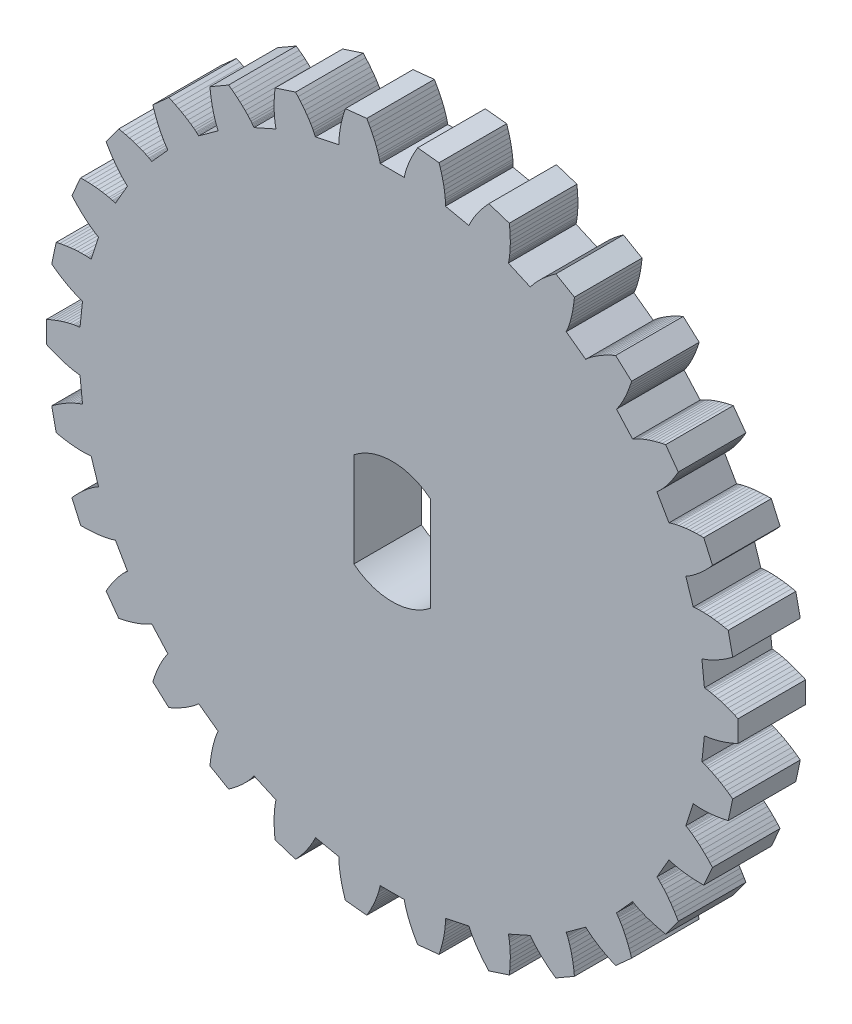
SolidWorks part; units mm, degrees
ref_plane "Front Plane" through (0, 0, 0) normal (0, 0, 1) x (1, 0, 0)
ref_plane "Top Plane" through (0, 0, 0) normal (0, 1, 0) x (1, 0, 0)
ref_plane "Right Plane" through (0, 0, 0) normal (1, 0, 0) x (0, 0, -1)
sketch "Model" plane through (0, 0, 0) normal (0, 0, 1) x (1, 0, 0)
  line L0 (29.209, 16.2732) -> (29.246, 16.2699)
  line L1 (29.246, 16.2699) -> (29.2831, 16.266)
  line L2 (29.2831, 16.266) -> (29.3202, 16.2615)
  line L3 (29.3202, 16.2615) -> (29.3573, 16.2565)
  line L4 (29.3573, 16.2565) -> (29.4317, 16.245)
  line L5 (29.4317, 16.245) -> (29.5061, 16.2317)
  line L6 (29.5061, 16.2317) -> (29.6552, 16.2001)
  line L7 (29.6552, 16.2001) -> (29.8045, 16.1625)
  line L8 (29.8045, 16.1625) -> (29.954, 16.1194)
  line L9 (29.954, 16.1194) -> (30.1035, 16.0712)
  line L10 (30.1035, 16.0712) -> (30.2531, 16.0181)
  line L11 (30.2531, 16.0181) -> (30.4025, 15.9603)
  line L12 (30.4025, 15.9603) -> (30.5519, 15.8981)
  line L13 (30.5519, 15.8981) -> (30.7012, 15.8315)
  line L14 (30.7012, 15.8315) -> (30.7012, 14.8771)
  line L15 (30.7012, 14.8771) -> (30.5519, 14.8105)
  line L16 (30.5519, 14.8105) -> (30.4025, 14.7482)
  line L17 (30.4025, 14.7482) -> (30.2531, 14.6905)
  line L18 (30.2531, 14.6905) -> (30.1035, 14.6374)
  line L19 (30.1035, 14.6374) -> (29.954, 14.5891)
  line L20 (29.954, 14.5891) -> (29.8045, 14.5461)
  line L21 (29.8045, 14.5461) -> (29.6552, 14.5085)
  line L22 (29.6552, 14.5085) -> (29.5061, 14.4769)
  line L23 (29.5061, 14.4769) -> (29.4317, 14.4636)
  line L24 (29.4317, 14.4636) -> (29.3573, 14.4521)
  line L25 (29.3573, 14.4521) -> (29.3202, 14.4471)
  line L26 (29.3202, 14.4471) -> (29.2831, 14.4426)
  line L27 (29.2831, 14.4426) -> (29.246, 14.4387)
  line L28 (29.246, 14.4387) -> (29.209, 14.4354)
  line L29 (29.209, 14.4354) -> (29.0973, 13.3725)
  line L30 (29.0973, 13.3725) -> (29.1328, 13.3616)
  line L31 (29.1328, 13.3616) -> (29.1683, 13.3501)
  line L32 (29.1683, 13.3501) -> (29.2036, 13.338)
  line L33 (29.2036, 13.338) -> (29.2389, 13.3254)
  line L34 (29.2389, 13.3254) -> (29.3092, 13.2987)
  line L35 (29.3092, 13.2987) -> (29.3793, 13.2702)
  line L36 (29.3793, 13.2702) -> (29.5185, 13.2083)
  line L37 (29.5185, 13.2083) -> (29.6568, 13.1405)
  line L38 (29.6568, 13.1405) -> (29.794, 13.0673)
  line L39 (29.794, 13.0673) -> (29.9303, 12.989)
  line L40 (29.9303, 12.989) -> (30.0655, 12.906)
  line L41 (30.0655, 12.906) -> (30.1997, 12.8184)
  line L42 (30.1997, 12.8184) -> (30.3329, 12.7264)
  line L43 (30.3329, 12.7264) -> (30.465, 12.6303)
  line L44 (30.465, 12.6303) -> (30.2666, 11.6967)
  line L45 (30.2666, 11.6967) -> (30.1068, 11.6626)
  line L46 (30.1068, 11.6626) -> (29.9477, 11.6328)
  line L47 (29.9477, 11.6328) -> (29.7895, 11.6074)
  line L48 (29.7895, 11.6074) -> (29.6321, 11.5865)
  line L49 (29.6321, 11.5865) -> (29.4759, 11.5704)
  line L50 (29.4759, 11.5704) -> (29.3207, 11.5594)
  line L51 (29.3207, 11.5594) -> (29.1668, 11.5536)
  line L52 (29.1668, 11.5536) -> (29.0144, 11.5537)
  line L53 (29.0144, 11.5537) -> (28.9389, 11.5562)
  line L54 (28.9389, 11.5562) -> (28.8637, 11.5604)
  line L55 (28.8637, 11.5604) -> (28.8264, 11.5632)
  line L56 (28.8264, 11.5632) -> (28.7892, 11.5666)
  line L57 (28.7892, 11.5666) -> (28.7521, 11.5704)
  line L58 (28.7521, 11.5704) -> (28.7152, 11.5749)
  line L59 (28.7152, 11.5749) -> (28.3849, 10.5585)
  line L60 (28.3849, 10.5585) -> (28.4174, 10.5404)
  line L61 (28.4174, 10.5404) -> (28.4497, 10.5218)
  line L62 (28.4497, 10.5218) -> (28.4818, 10.5026)
  line L63 (28.4818, 10.5026) -> (28.5137, 10.4829)
  line L64 (28.5137, 10.4829) -> (28.5769, 10.4422)
  line L65 (28.5769, 10.4422) -> (28.6395, 10.3998)
  line L66 (28.6395, 10.3998) -> (28.7628, 10.3103)
  line L67 (28.7628, 10.3103) -> (28.884, 10.2152)
  line L68 (28.884, 10.2152) -> (29.003, 10.115)
  line L69 (29.003, 10.115) -> (29.12, 10.0102)
  line L70 (29.12, 10.0102) -> (29.235, 9.9008)
  line L71 (29.235, 9.9008) -> (29.3481, 9.7873)
  line L72 (29.3481, 9.7873) -> (29.4592, 9.6696)
  line L73 (29.4592, 9.6696) -> (29.5684, 9.5481)
  line L74 (29.5684, 9.5481) -> (29.1802, 8.6762)
  line L75 (29.1802, 8.6762) -> (29.0168, 8.6761)
  line L76 (29.0168, 8.6761) -> (28.8551, 8.68)
  line L77 (28.8551, 8.68) -> (28.695, 8.688)
  line L78 (28.695, 8.688) -> (28.5368, 8.7003)
  line L79 (28.5368, 8.7003) -> (28.3806, 8.7171)
  line L80 (28.3806, 8.7171) -> (28.2265, 8.7385)
  line L81 (28.2265, 8.7385) -> (28.0748, 8.7649)
  line L82 (28.0748, 8.7649) -> (27.9257, 8.7967)
  line L83 (27.9257, 8.7967) -> (27.8523, 8.8148)
  line L84 (27.8523, 8.8148) -> (27.7797, 8.8345)
  line L85 (27.7797, 8.8345) -> (27.7438, 8.8451)
  line L86 (27.7438, 8.8451) -> (27.7081, 8.8561)
  line L87 (27.7081, 8.8561) -> (27.6726, 8.8676)
  line L88 (27.6726, 8.8676) -> (27.6375, 8.8796)
  line L89 (27.6375, 8.8796) -> (27.1031, 7.9541)
  line L90 (27.1031, 7.9541) -> (27.1311, 7.9296)
  line L91 (27.1311, 7.9296) -> (27.1588, 7.9047)
  line L92 (27.1588, 7.9047) -> (27.1862, 7.8793)
  line L93 (27.1862, 7.8793) -> (27.2133, 7.8534)
  line L94 (27.2133, 7.8534) -> (27.2667, 7.8004)
  line L95 (27.2667, 7.8004) -> (27.3191, 7.7459)
  line L96 (27.3191, 7.7459) -> (27.4211, 7.6327)
  line L97 (27.4211, 7.6327) -> (27.5198, 7.5145)
  line L98 (27.5198, 7.5145) -> (27.6154, 7.3918)
  line L99 (27.6154, 7.3918) -> (27.708, 7.2649)
  line L100 (27.708, 7.2649) -> (27.7978, 7.134)
  line L101 (27.7978, 7.134) -> (27.8848, 6.9994)
  line L102 (27.8848, 6.9994) -> (27.9691, 6.8613)
  line L103 (27.9691, 6.8613) -> (28.0507, 6.7197)
  line L104 (28.0507, 6.7197) -> (27.4897, 5.9476)
  line L105 (27.4897, 5.9476) -> (27.3298, 5.9814)
  line L106 (27.3298, 5.9814) -> (27.1724, 6.0188)
  line L107 (27.1724, 6.0188) -> (27.0175, 6.06)
  line L108 (27.0175, 6.06) -> (26.8653, 6.1049)
  line L109 (26.8653, 6.1049) -> (26.7159, 6.1538)
  line L110 (26.7159, 6.1538) -> (26.5697, 6.2068)
  line L111 (26.5697, 6.2068) -> (26.4268, 6.2641)
  line L112 (26.4268, 6.2641) -> (26.2876, 6.3262)
  line L113 (26.2876, 6.3262) -> (26.2196, 6.3592)
  line L114 (26.2196, 6.3592) -> (26.1527, 6.3936)
  line L115 (26.1527, 6.3936) -> (26.1197, 6.4114)
  line L116 (26.1197, 6.4114) -> (26.0871, 6.4296)
  line L117 (26.0871, 6.4296) -> (26.0548, 6.4482)
  line L118 (26.0548, 6.4482) -> (26.0229, 6.4673)
  line L119 (26.0229, 6.4673) -> (25.3078, 5.6731)
  line L120 (25.3078, 5.6731) -> (25.3301, 5.6433)
  line L121 (25.3301, 5.6433) -> (25.352, 5.6132)
  line L122 (25.352, 5.6132) -> (25.3735, 5.5826)
  line L123 (25.3735, 5.5826) -> (25.3946, 5.5517)
  line L124 (25.3946, 5.5517) -> (25.4358, 5.4888)
  line L125 (25.4358, 5.4888) -> (25.4757, 5.4245)
  line L126 (25.4757, 5.4245) -> (25.552, 5.2926)
  line L127 (25.552, 5.2926) -> (25.624, 5.1565)
  line L128 (25.624, 5.1565) -> (25.692, 5.0166)
  line L129 (25.692, 5.0166) -> (25.7562, 4.8732)
  line L130 (25.7562, 4.8732) -> (25.8168, 4.7265)
  line L131 (25.8168, 4.7265) -> (25.8739, 4.5768)
  line L132 (25.8739, 4.5768) -> (25.9276, 4.4241)
  line L133 (25.9276, 4.4241) -> (25.978, 4.2687)
  line L134 (25.978, 4.2687) -> (25.2687, 3.63)
  line L135 (25.2687, 3.63) -> (25.1194, 3.6964)
  line L136 (25.1194, 3.6964) -> (24.9732, 3.7657)
  line L137 (24.9732, 3.7657) -> (24.8302, 3.8382)
  line L138 (24.8302, 3.8382) -> (24.6907, 3.9138)
  line L139 (24.6907, 3.9138) -> (24.5548, 3.9926)
  line L140 (24.5548, 3.9926) -> (24.4227, 4.0749)
  line L141 (24.4227, 4.0749) -> (24.2949, 4.1607)
  line L142 (24.2949, 4.1607) -> (24.1717, 4.2503)
  line L143 (24.1717, 4.2503) -> (24.112, 4.2968)
  line L144 (24.112, 4.2968) -> (24.0537, 4.3443)
  line L145 (24.0537, 4.3443) -> (24.0251, 4.3685)
  line L146 (24.0251, 4.3685) -> (23.997, 4.3931)
  line L147 (23.997, 4.3931) -> (23.9693, 4.4181)
  line L148 (23.9693, 4.4181) -> (23.9421, 4.4434)
  line L149 (23.9421, 4.4434) -> (23.0774, 3.8152)
  line L150 (23.0774, 3.8152) -> (23.0931, 3.7815)
  line L151 (23.0931, 3.7815) -> (23.1082, 3.7474)
  line L152 (23.1082, 3.7474) -> (23.1229, 3.7131)
  line L153 (23.1229, 3.7131) -> (23.1371, 3.6784)
  line L154 (23.1371, 3.6784) -> (23.1644, 3.6083)
  line L155 (23.1644, 3.6083) -> (23.19, 3.5372)
  line L156 (23.19, 3.5372) -> (23.2372, 3.3922)
  line L157 (23.2372, 3.3922) -> (23.2793, 3.2441)
  line L158 (23.2793, 3.2441) -> (23.3168, 3.0932)
  line L159 (23.3168, 3.0932) -> (23.3498, 2.9395)
  line L160 (23.3498, 2.9395) -> (23.3785, 2.7835)
  line L161 (23.3785, 2.7835) -> (23.4033, 2.6251)
  line L162 (23.4033, 2.6251) -> (23.4241, 2.4646)
  line L163 (23.4241, 2.4646) -> (23.441, 2.3021)
  line L164 (23.441, 2.3021) -> (22.6144, 1.8249)
  line L165 (22.6144, 1.8249) -> (22.4822, 1.9208)
  line L166 (22.4822, 1.9208) -> (22.3536, 2.0191)
  line L167 (22.3536, 2.0191) -> (22.2288, 2.1197)
  line L168 (22.2288, 2.1197) -> (22.108, 2.2226)
  line L169 (22.108, 2.2226) -> (21.9915, 2.328)
  line L170 (21.9915, 2.328) -> (21.8795, 2.4359)
  line L171 (21.8795, 2.4359) -> (21.7722, 2.5464)
  line L172 (21.7722, 2.5464) -> (21.6703, 2.6598)
  line L173 (21.6703, 2.6598) -> (21.6216, 2.7176)
  line L174 (21.6216, 2.7176) -> (21.5745, 2.7762)
  line L175 (21.5745, 2.7762) -> (21.5516, 2.8058)
  line L176 (21.5516, 2.8058) -> (21.5292, 2.8357)
  line L177 (21.5292, 2.8357) -> (21.5072, 2.8659)
  line L178 (21.5072, 2.8659) -> (21.4859, 2.8963)
  line L179 (21.4859, 2.8963) -> (20.5095, 2.4616)
  line L180 (20.5095, 2.4616) -> (20.5178, 2.4254)
  line L181 (20.5178, 2.4254) -> (20.5256, 2.3889)
  line L182 (20.5256, 2.3889) -> (20.5328, 2.3523)
  line L183 (20.5328, 2.3523) -> (20.5395, 2.3154)
  line L184 (20.5395, 2.3154) -> (20.5516, 2.2411)
  line L185 (20.5516, 2.2411) -> (20.5619, 2.1662)
  line L186 (20.5619, 2.1662) -> (20.5779, 2.0147)
  line L187 (20.5779, 2.0147) -> (20.5883, 1.8611)
  line L188 (20.5883, 1.8611) -> (20.5935, 1.7056)
  line L189 (20.5935, 1.7056) -> (20.5939, 1.5485)
  line L190 (20.5939, 1.5485) -> (20.5896, 1.3898)
  line L191 (20.5896, 1.3898) -> (20.5808, 1.2298)
  line L192 (20.5808, 1.2298) -> (20.5678, 1.0685)
  line L193 (20.5678, 1.0685) -> (20.5506, 0.906)
  line L194 (20.5506, 0.906) -> (19.6429, 0.6111)
  line L195 (19.6429, 0.6111) -> (19.5334, 0.7324)
  line L196 (19.5334, 0.7324) -> (19.4281, 0.8553)
  line L197 (19.4281, 0.8553) -> (19.3269, 0.9796)
  line L198 (19.3269, 0.9796) -> (19.2302, 1.1054)
  line L199 (19.2302, 1.1054) -> (19.1381, 1.2327)
  line L200 (19.1381, 1.2327) -> (19.051, 1.3615)
  line L201 (19.051, 1.3615) -> (18.9691, 1.4919)
  line L202 (18.9691, 1.4919) -> (18.893, 1.624)
  line L203 (18.893, 1.624) -> (18.8573, 1.6907)
  line L204 (18.8573, 1.6907) -> (18.8234, 1.7578)
  line L205 (18.8234, 1.7578) -> (18.8072, 1.7916)
  line L206 (18.8072, 1.7916) -> (18.7915, 1.8255)
  line L207 (18.7915, 1.8255) -> (18.7763, 1.8595)
  line L208 (18.7763, 1.8595) -> (18.7617, 1.8937)
  line L209 (18.7617, 1.8937) -> (17.7163, 1.6715)
  line L210 (17.7163, 1.6715) -> (17.7169, 1.6343)
  line L211 (17.7169, 1.6343) -> (17.7169, 1.5971)
  line L212 (17.7169, 1.5971) -> (17.7164, 1.5597)
  line L213 (17.7164, 1.5597) -> (17.7153, 1.5223)
  line L214 (17.7153, 1.5223) -> (17.7116, 1.4471)
  line L215 (17.7116, 1.4471) -> (17.7061, 1.3717)
  line L216 (17.7061, 1.3717) -> (17.6903, 1.2201)
  line L217 (17.6903, 1.2201) -> (17.6685, 1.0677)
  line L218 (17.6685, 1.0677) -> (17.6413, 0.9146)
  line L219 (17.6413, 0.9146) -> (17.609, 0.7608)
  line L220 (17.609, 0.7608) -> (17.5718, 0.6065)
  line L221 (17.5718, 0.6065) -> (17.53, 0.4518)
  line L222 (17.53, 0.4518) -> (17.4837, 0.2967)
  line L223 (17.4837, 0.2967) -> (17.4331, 0.1414)
  line L224 (17.4331, 0.1414) -> (16.4839, 0.0416)
  line L225 (16.4839, 0.0416) -> (16.402, 0.183)
  line L226 (16.402, 0.183) -> (16.3245, 0.3251)
  line L227 (16.3245, 0.3251) -> (16.2515, 0.4677)
  line L228 (16.2515, 0.4677) -> (16.183, 0.6109)
  line L229 (16.183, 0.6109) -> (16.1194, 0.7546)
  line L230 (16.1194, 0.7546) -> (16.0609, 0.8987)
  line L231 (16.0609, 0.8987) -> (16.008, 1.0433)
  line L232 (16.008, 1.0433) -> (15.961, 1.1883)
  line L233 (15.961, 1.1883) -> (15.9399, 1.2609)
  line L234 (15.9399, 1.2609) -> (15.9207, 1.3336)
  line L235 (15.9207, 1.3336) -> (15.9119, 1.3701)
  line L236 (15.9119, 1.3701) -> (15.9036, 1.4065)
  line L237 (15.9036, 1.4065) -> (15.8958, 1.4429)
  line L238 (15.8958, 1.4429) -> (15.8887, 1.4794)
  line L239 (15.8887, 1.4794) -> (14.8199, 1.4794)
  line L240 (14.8199, 1.4794) -> (14.8128, 1.4429)
  line L241 (14.8128, 1.4429) -> (14.805, 1.4065)
  line L242 (14.805, 1.4065) -> (14.7967, 1.3701)
  line L243 (14.7967, 1.3701) -> (14.7878, 1.3336)
  line L244 (14.7878, 1.3336) -> (14.7686, 1.2609)
  line L245 (14.7686, 1.2609) -> (14.7476, 1.1883)
  line L246 (14.7476, 1.1883) -> (14.7006, 1.0433)
  line L247 (14.7006, 1.0433) -> (14.6476, 0.8987)
  line L248 (14.6476, 0.8987) -> (14.5891, 0.7546)
  line L249 (14.5891, 0.7546) -> (14.5256, 0.6109)
  line L250 (14.5256, 0.6109) -> (14.4571, 0.4677)
  line L251 (14.4571, 0.4677) -> (14.384, 0.3251)
  line L252 (14.384, 0.3251) -> (14.3065, 0.183)
  line L253 (14.3065, 0.183) -> (14.2247, 0.0416)
  line L254 (14.2247, 0.0416) -> (13.2755, 0.1414)
  line L255 (13.2755, 0.1414) -> (13.2249, 0.2967)
  line L256 (13.2249, 0.2967) -> (13.1786, 0.4518)
  line L257 (13.1786, 0.4518) -> (13.1368, 0.6065)
  line L258 (13.1368, 0.6065) -> (13.0996, 0.7608)
  line L259 (13.0996, 0.7608) -> (13.0673, 0.9146)
  line L260 (13.0673, 0.9146) -> (13.04, 1.0677)
  line L261 (13.04, 1.0677) -> (13.0183, 1.2201)
  line L262 (13.0183, 1.2201) -> (13.0024, 1.3717)
  line L263 (13.0024, 1.3717) -> (12.997, 1.4471)
  line L264 (12.997, 1.4471) -> (12.9933, 1.5223)
  line L265 (12.9933, 1.5223) -> (12.9922, 1.5597)
  line L266 (12.9922, 1.5597) -> (12.9916, 1.5971)
  line L267 (12.9916, 1.5971) -> (12.9916, 1.6343)
  line L268 (12.9916, 1.6343) -> (12.9922, 1.6715)
  line L269 (12.9922, 1.6715) -> (11.9468, 1.8937)
  line L270 (11.9468, 1.8937) -> (11.9323, 1.8595)
  line L271 (11.9323, 1.8595) -> (11.9171, 1.8255)
  line L272 (11.9171, 1.8255) -> (11.9014, 1.7916)
  line L273 (11.9014, 1.7916) -> (11.8852, 1.7578)
  line L274 (11.8852, 1.7578) -> (11.8513, 1.6907)
  line L275 (11.8513, 1.6907) -> (11.8156, 1.624)
  line L276 (11.8156, 1.624) -> (11.7395, 1.4919)
  line L277 (11.7395, 1.4919) -> (11.6576, 1.3615)
  line L278 (11.6576, 1.3615) -> (11.5704, 1.2327)
  line L279 (11.5704, 1.2327) -> (11.4783, 1.1054)
  line L280 (11.4783, 1.1054) -> (11.3816, 0.9796)
  line L281 (11.3816, 0.9796) -> (11.2805, 0.8553)
  line L282 (11.2805, 0.8553) -> (11.1751, 0.7324)
  line L283 (11.1751, 0.7324) -> (11.0657, 0.6111)
  line L284 (11.0657, 0.6111) -> (10.158, 0.906)
  line L285 (10.158, 0.906) -> (10.1408, 1.0685)
  line L286 (10.1408, 1.0685) -> (10.1277, 1.2298)
  line L287 (10.1277, 1.2298) -> (10.119, 1.3898)
  line L288 (10.119, 1.3898) -> (10.1147, 1.5485)
  line L289 (10.1147, 1.5485) -> (10.115, 1.7056)
  line L290 (10.115, 1.7056) -> (10.1203, 1.8611)
  line L291 (10.1203, 1.8611) -> (10.1306, 2.0147)
  line L292 (10.1306, 2.0147) -> (10.1467, 2.1662)
  line L293 (10.1467, 2.1662) -> (10.157, 2.2411)
  line L294 (10.157, 2.2411) -> (10.1691, 2.3154)
  line L295 (10.1691, 2.3154) -> (10.1758, 2.3523)
  line L296 (10.1758, 2.3523) -> (10.183, 2.3889)
  line L297 (10.183, 2.3889) -> (10.1907, 2.4254)
  line L298 (10.1907, 2.4254) -> (10.199, 2.4616)
  line L299 (10.199, 2.4616) -> (9.2227, 2.8963)
  line L300 (9.2227, 2.8963) -> (9.2013, 2.8659)
  line L301 (9.2013, 2.8659) -> (9.1794, 2.8357)
  line L302 (9.1794, 2.8357) -> (9.157, 2.8058)
  line L303 (9.157, 2.8058) -> (9.1341, 2.7762)
  line L304 (9.1341, 2.7762) -> (9.087, 2.7176)
  line L305 (9.087, 2.7176) -> (9.0382, 2.6598)
  line L306 (9.0382, 2.6598) -> (8.9363, 2.5464)
  line L307 (8.9363, 2.5464) -> (8.8291, 2.4359)
  line L308 (8.8291, 2.4359) -> (8.7171, 2.328)
  line L309 (8.7171, 2.328) -> (8.6005, 2.2226)
  line L310 (8.6005, 2.2226) -> (8.4798, 2.1197)
  line L311 (8.4798, 2.1197) -> (8.355, 2.0191)
  line L312 (8.355, 2.0191) -> (8.2264, 1.9208)
  line L313 (8.2264, 1.9208) -> (8.0941, 1.8249)
  line L314 (8.0941, 1.8249) -> (7.2676, 2.3021)
  line L315 (7.2676, 2.3021) -> (7.2845, 2.4646)
  line L316 (7.2845, 2.4646) -> (7.3053, 2.6251)
  line L317 (7.3053, 2.6251) -> (7.33, 2.7835)
  line L318 (7.33, 2.7835) -> (7.3588, 2.9395)
  line L319 (7.3588, 2.9395) -> (7.3918, 3.0932)
  line L320 (7.3918, 3.0932) -> (7.4292, 3.2441)
  line L321 (7.4292, 3.2441) -> (7.4713, 3.3922)
  line L322 (7.4713, 3.3922) -> (7.5185, 3.5372)
  line L323 (7.5185, 3.5372) -> (7.5442, 3.6083)
  line L324 (7.5442, 3.6083) -> (7.5714, 3.6784)
  line L325 (7.5714, 3.6784) -> (7.5857, 3.7131)
  line L326 (7.5857, 3.7131) -> (7.6003, 3.7474)
  line L327 (7.6003, 3.7474) -> (7.6155, 3.7815)
  line L328 (7.6155, 3.7815) -> (7.6312, 3.8152)
  line L329 (7.6312, 3.8152) -> (6.7665, 4.4434)
  line L330 (6.7665, 4.4434) -> (6.7393, 4.4181)
  line L331 (6.7393, 4.4181) -> (6.7116, 4.3931)
  line L332 (6.7116, 4.3931) -> (6.6835, 4.3685)
  line L333 (6.6835, 4.3685) -> (6.6549, 4.3443)
  line L334 (6.6549, 4.3443) -> (6.5966, 4.2968)
  line L335 (6.5966, 4.2968) -> (6.5369, 4.2503)
  line L336 (6.5369, 4.2503) -> (6.4137, 4.1607)
  line L337 (6.4137, 4.1607) -> (6.2858, 4.0749)
  line L338 (6.2858, 4.0749) -> (6.1538, 3.9926)
  line L339 (6.1538, 3.9926) -> (6.0179, 3.9138)
  line L340 (6.0179, 3.9138) -> (5.8784, 3.8382)
  line L341 (5.8784, 3.8382) -> (5.7354, 3.7657)
  line L342 (5.7354, 3.7657) -> (5.5892, 3.6964)
  line L343 (5.5892, 3.6964) -> (5.4399, 3.63)
  line L344 (5.4399, 3.63) -> (4.7306, 4.2687)
  line L345 (4.7306, 4.2687) -> (4.7809, 4.4241)
  line L346 (4.7809, 4.4241) -> (4.8346, 4.5768)
  line L347 (4.8346, 4.5768) -> (4.8918, 4.7265)
  line L348 (4.8918, 4.7265) -> (4.9524, 4.8732)
  line L349 (4.9524, 4.8732) -> (5.0166, 5.0166)
  line L350 (5.0166, 5.0166) -> (5.0846, 5.1565)
  line L351 (5.0846, 5.1565) -> (5.1565, 5.2926)
  line L352 (5.1565, 5.2926) -> (5.2328, 5.4245)
  line L353 (5.2328, 5.4245) -> (5.2728, 5.4888)
  line L354 (5.2728, 5.4888) -> (5.314, 5.5517)
  line L355 (5.314, 5.5517) -> (5.3351, 5.5826)
  line L356 (5.3351, 5.5826) -> (5.3566, 5.6132)
  line L357 (5.3566, 5.6132) -> (5.3785, 5.6433)
  line L358 (5.3785, 5.6433) -> (5.4008, 5.6731)
  line L359 (5.4008, 5.6731) -> (4.6857, 6.4673)
  line L360 (4.6857, 6.4673) -> (4.6538, 6.4482)
  line L361 (4.6538, 6.4482) -> (4.6215, 6.4296)
  line L362 (4.6215, 6.4296) -> (4.5889, 6.4114)
  line L363 (4.5889, 6.4114) -> (4.5559, 6.3936)
  line L364 (4.5559, 6.3936) -> (4.489, 6.3592)
  line L365 (4.489, 6.3592) -> (4.4209, 6.3262)
  line L366 (4.4209, 6.3262) -> (4.2818, 6.2641)
  line L367 (4.2818, 6.2641) -> (4.1389, 6.2068)
  line L368 (4.1389, 6.2068) -> (3.9926, 6.1538)
  line L369 (3.9926, 6.1538) -> (3.8433, 6.1049)
  line L370 (3.8433, 6.1049) -> (3.6911, 6.06)
  line L371 (3.6911, 6.06) -> (3.5362, 6.0188)
  line L372 (3.5362, 6.0188) -> (3.3788, 5.9814)
  line L373 (3.3788, 5.9814) -> (3.2189, 5.9476)
  line L374 (3.2189, 5.9476) -> (2.6579, 6.7197)
  line L375 (2.6579, 6.7197) -> (2.7395, 6.8613)
  line L376 (2.7395, 6.8613) -> (2.8238, 6.9994)
  line L377 (2.8238, 6.9994) -> (2.9108, 7.134)
  line L378 (2.9108, 7.134) -> (3.0005, 7.2649)
  line L379 (3.0005, 7.2649) -> (3.0932, 7.3918)
  line L380 (3.0932, 7.3918) -> (3.1887, 7.5145)
  line L381 (3.1887, 7.5145) -> (3.2875, 7.6327)
  line L382 (3.2875, 7.6327) -> (3.3895, 7.7459)
  line L383 (3.3895, 7.7459) -> (3.4419, 7.8004)
  line L384 (3.4419, 7.8004) -> (3.4953, 7.8534)
  line L385 (3.4953, 7.8534) -> (3.5224, 7.8793)
  line L386 (3.5224, 7.8793) -> (3.5498, 7.9047)
  line L387 (3.5498, 7.9047) -> (3.5775, 7.9296)
  line L388 (3.5775, 7.9296) -> (3.6055, 7.9541)
  line L389 (3.6055, 7.9541) -> (3.0711, 8.8796)
  line L390 (3.0711, 8.8796) -> (3.0359, 8.8676)
  line L391 (3.0359, 8.8676) -> (3.0005, 8.8561)
  line L392 (3.0005, 8.8561) -> (2.9648, 8.8451)
  line L393 (2.9648, 8.8451) -> (2.9288, 8.8345)
  line L394 (2.9288, 8.8345) -> (2.8562, 8.8148)
  line L395 (2.8562, 8.8148) -> (2.7828, 8.7967)
  line L396 (2.7828, 8.7967) -> (2.6338, 8.7649)
  line L397 (2.6338, 8.7649) -> (2.4821, 8.7385)
  line L398 (2.4821, 8.7385) -> (2.328, 8.7171)
  line L399 (2.328, 8.7171) -> (2.1718, 8.7003)
  line L400 (2.1718, 8.7003) -> (2.0136, 8.688)
  line L401 (2.0136, 8.688) -> (1.8535, 8.68)
  line L402 (1.8535, 8.68) -> (1.6917, 8.6761)
  line L403 (1.6917, 8.6761) -> (1.5283, 8.6762)
  line L404 (1.5283, 8.6762) -> (1.1401, 9.5481)
  line L405 (1.1401, 9.5481) -> (1.2494, 9.6696)
  line L406 (1.2494, 9.6696) -> (1.3605, 9.7873)
  line L407 (1.3605, 9.7873) -> (1.4736, 9.9008)
  line L408 (1.4736, 9.9008) -> (1.5886, 10.0102)
  line L409 (1.5886, 10.0102) -> (1.7056, 10.115)
  line L410 (1.7056, 10.115) -> (1.8246, 10.2152)
  line L411 (1.8246, 10.2152) -> (1.9457, 10.3103)
  line L412 (1.9457, 10.3103) -> (2.0691, 10.3998)
  line L413 (2.0691, 10.3998) -> (2.1317, 10.4422)
  line L414 (2.1317, 10.4422) -> (2.1949, 10.4829)
  line L415 (2.1949, 10.4829) -> (2.2268, 10.5026)
  line L416 (2.2268, 10.5026) -> (2.2589, 10.5218)
  line L417 (2.2589, 10.5218) -> (2.2911, 10.5404)
  line L418 (2.2911, 10.5404) -> (2.3236, 10.5585)
  line L419 (2.3236, 10.5585) -> (1.9934, 11.5749)
  line L420 (1.9934, 11.5749) -> (1.9565, 11.5704)
  line L421 (1.9565, 11.5704) -> (1.9194, 11.5666)
  line L422 (1.9194, 11.5666) -> (1.8822, 11.5632)
  line L423 (1.8822, 11.5632) -> (1.8448, 11.5604)
  line L424 (1.8448, 11.5604) -> (1.7697, 11.5562)
  line L425 (1.7697, 11.5562) -> (1.6941, 11.5537)
  line L426 (1.6941, 11.5537) -> (1.5417, 11.5536)
  line L427 (1.5417, 11.5536) -> (1.3879, 11.5594)
  line L428 (1.3879, 11.5594) -> (1.2327, 11.5704)
  line L429 (1.2327, 11.5704) -> (1.0764, 11.5865)
  line L430 (1.0764, 11.5865) -> (0.9191, 11.6074)
  line L431 (0.9191, 11.6074) -> (0.7609, 11.6328)
  line L432 (0.7609, 11.6328) -> (0.6018, 11.6626)
  line L433 (0.6018, 11.6626) -> (0.442, 11.6967)
  line L434 (0.442, 11.6967) -> (0.2436, 12.6303)
  line L435 (0.2436, 12.6303) -> (0.3757, 12.7264)
  line L436 (0.3757, 12.7264) -> (0.5089, 12.8184)
  line L437 (0.5089, 12.8184) -> (0.6431, 12.906)
  line L438 (0.6431, 12.906) -> (0.7783, 12.989)
  line L439 (0.7783, 12.989) -> (0.9146, 13.0673)
  line L440 (0.9146, 13.0673) -> (1.0518, 13.1405)
  line L441 (1.0518, 13.1405) -> (1.19, 13.2083)
  line L442 (1.19, 13.2083) -> (1.3293, 13.2702)
  line L443 (1.3293, 13.2702) -> (1.3993, 13.2987)
  line L444 (1.3993, 13.2987) -> (1.4697, 13.3254)
  line L445 (1.4697, 13.3254) -> (1.5049, 13.338)
  line L446 (1.5049, 13.338) -> (1.5403, 13.3501)
  line L447 (1.5403, 13.3501) -> (1.5757, 13.3616)
  line L448 (1.5757, 13.3616) -> (1.6113, 13.3725)
  line L449 (1.6113, 13.3725) -> (1.4996, 14.4354)
  line L450 (1.4996, 14.4354) -> (1.4625, 14.4387)
  line L451 (1.4625, 14.4387) -> (1.4255, 14.4426)
  line L452 (1.4255, 14.4426) -> (1.3884, 14.4471)
  line L453 (1.3884, 14.4471) -> (1.3512, 14.4521)
  line L454 (1.3512, 14.4521) -> (1.2769, 14.4636)
  line L455 (1.2769, 14.4636) -> (1.2025, 14.4769)
  line L456 (1.2025, 14.4769) -> (1.0534, 14.5085)
  line L457 (1.0534, 14.5085) -> (0.9041, 14.5461)
  line L458 (0.9041, 14.5461) -> (0.7546, 14.5891)
  line L459 (0.7546, 14.5891) -> (0.6051, 14.6374)
  line L460 (0.6051, 14.6374) -> (0.4555, 14.6905)
  line L461 (0.4555, 14.6905) -> (0.306, 14.7482)
  line L462 (0.306, 14.7482) -> (0.1566, 14.8105)
  line L463 (0.1566, 14.8105) -> (0.0074, 14.8771)
  line L464 (0.0074, 14.8771) -> (0.0074, 15.8315)
  line L465 (0.0074, 15.8315) -> (0.1566, 15.8981)
  line L466 (0.1566, 15.8981) -> (0.306, 15.9603)
  line L467 (0.306, 15.9603) -> (0.4555, 16.0181)
  line L468 (0.4555, 16.0181) -> (0.6051, 16.0712)
  line L469 (0.6051, 16.0712) -> (0.7546, 16.1194)
  line L470 (0.7546, 16.1194) -> (0.9041, 16.1625)
  line L471 (0.9041, 16.1625) -> (1.0534, 16.2001)
  line L472 (1.0534, 16.2001) -> (1.2025, 16.2317)
  line L473 (1.2025, 16.2317) -> (1.2769, 16.245)
  line L474 (1.2769, 16.245) -> (1.3512, 16.2565)
  line L475 (1.3512, 16.2565) -> (1.3884, 16.2615)
  line L476 (1.3884, 16.2615) -> (1.4255, 16.266)
  line L477 (1.4255, 16.266) -> (1.4625, 16.2699)
  line L478 (1.4625, 16.2699) -> (1.4996, 16.2732)
  line L479 (1.4996, 16.2732) -> (1.6113, 17.3361)
  line L480 (1.6113, 17.3361) -> (1.5757, 17.347)
  line L481 (1.5757, 17.347) -> (1.5403, 17.3585)
  line L482 (1.5403, 17.3585) -> (1.5049, 17.3706)
  line L483 (1.5049, 17.3706) -> (1.4697, 17.3832)
  line L484 (1.4697, 17.3832) -> (1.3993, 17.4099)
  line L485 (1.3993, 17.4099) -> (1.3293, 17.4384)
  line L486 (1.3293, 17.4384) -> (1.19, 17.5003)
  line L487 (1.19, 17.5003) -> (1.0518, 17.5681)
  line L488 (1.0518, 17.5681) -> (0.9146, 17.6413)
  line L489 (0.9146, 17.6413) -> (0.7783, 17.7196)
  line L490 (0.7783, 17.7196) -> (0.6431, 17.8026)
  line L491 (0.6431, 17.8026) -> (0.5089, 17.8902)
  line L492 (0.5089, 17.8902) -> (0.3757, 17.9821)
  line L493 (0.3757, 17.9821) -> (0.2436, 18.0783)
  line L494 (0.2436, 18.0783) -> (0.442, 19.0119)
  line L495 (0.442, 19.0119) -> (0.6018, 19.046)
  line L496 (0.6018, 19.046) -> (0.7609, 19.0758)
  line L497 (0.7609, 19.0758) -> (0.9191, 19.1012)
  line L498 (0.9191, 19.1012) -> (1.0764, 19.1221)
  line L499 (1.0764, 19.1221) -> (1.2327, 19.1381)
  line L500 (1.2327, 19.1381) -> (1.3879, 19.1492)
  line L501 (1.3879, 19.1492) -> (1.5417, 19.1549)
  line L502 (1.5417, 19.1549) -> (1.6941, 19.1548)
  line L503 (1.6941, 19.1548) -> (1.7697, 19.1524)
  line L504 (1.7697, 19.1524) -> (1.8448, 19.1482)
  line L505 (1.8448, 19.1482) -> (1.8822, 19.1453)
  line L506 (1.8822, 19.1453) -> (1.9194, 19.142)
  line L507 (1.9194, 19.142) -> (1.9565, 19.1381)
  line L508 (1.9565, 19.1381) -> (1.9934, 19.1336)
  line L509 (1.9934, 19.1336) -> (2.3236, 20.1501)
  line L510 (2.3236, 20.1501) -> (2.2911, 20.1681)
  line L511 (2.2911, 20.1681) -> (2.2589, 20.1868)
  line L512 (2.2589, 20.1868) -> (2.2268, 20.206)
  line L513 (2.2268, 20.206) -> (2.1949, 20.2256)
  line L514 (2.1949, 20.2256) -> (2.1317, 20.2664)
  line L515 (2.1317, 20.2664) -> (2.0691, 20.3088)
  line L516 (2.0691, 20.3088) -> (1.9457, 20.3983)
  line L517 (1.9457, 20.3983) -> (1.8246, 20.4934)
  line L518 (1.8246, 20.4934) -> (1.7056, 20.5935)
  line L519 (1.7056, 20.5935) -> (1.5886, 20.6984)
  line L520 (1.5886, 20.6984) -> (1.4736, 20.8077)
  line L521 (1.4736, 20.8077) -> (1.3605, 20.9213)
  line L522 (1.3605, 20.9213) -> (1.2494, 21.0389)
  line L523 (1.2494, 21.0389) -> (1.1401, 21.1605)
  line L524 (1.1401, 21.1605) -> (1.5283, 22.0324)
  line L525 (1.5283, 22.0324) -> (1.6917, 22.0325)
  line L526 (1.6917, 22.0325) -> (1.8535, 22.0286)
  line L527 (1.8535, 22.0286) -> (2.0136, 22.0206)
  line L528 (2.0136, 22.0206) -> (2.1718, 22.0083)
  line L529 (2.1718, 22.0083) -> (2.328, 21.9915)
  line L530 (2.328, 21.9915) -> (2.4821, 21.9701)
  line L531 (2.4821, 21.9701) -> (2.6338, 21.9437)
  line L532 (2.6338, 21.9437) -> (2.7828, 21.9119)
  line L533 (2.7828, 21.9119) -> (2.8562, 21.8938)
  line L534 (2.8562, 21.8938) -> (2.9288, 21.874)
  line L535 (2.9288, 21.874) -> (2.9648, 21.8635)
  line L536 (2.9648, 21.8635) -> (3.0005, 21.8525)
  line L537 (3.0005, 21.8525) -> (3.0359, 21.841)
  line L538 (3.0359, 21.841) -> (3.0711, 21.8289)
  line L539 (3.0711, 21.8289) -> (3.6055, 22.7545)
  line L540 (3.6055, 22.7545) -> (3.5775, 22.7789)
  line L541 (3.5775, 22.7789) -> (3.5498, 22.8039)
  line L542 (3.5498, 22.8039) -> (3.5224, 22.8293)
  line L543 (3.5224, 22.8293) -> (3.4953, 22.8552)
  line L544 (3.4953, 22.8552) -> (3.4419, 22.9082)
  line L545 (3.4419, 22.9082) -> (3.3895, 22.9627)
  line L546 (3.3895, 22.9627) -> (3.2875, 23.0759)
  line L547 (3.2875, 23.0759) -> (3.1887, 23.194)
  line L548 (3.1887, 23.194) -> (3.0932, 23.3168)
  line L549 (3.0932, 23.3168) -> (3.0005, 23.4437)
  line L550 (3.0005, 23.4437) -> (2.9108, 23.5745)
  line L551 (2.9108, 23.5745) -> (2.8238, 23.7091)
  line L552 (2.8238, 23.7091) -> (2.7395, 23.8473)
  line L553 (2.7395, 23.8473) -> (2.6579, 23.9889)
  line L554 (2.6579, 23.9889) -> (3.2189, 24.761)
  line L555 (3.2189, 24.761) -> (3.3788, 24.7272)
  line L556 (3.3788, 24.7272) -> (3.5362, 24.6897)
  line L557 (3.5362, 24.6897) -> (3.6911, 24.6486)
  line L558 (3.6911, 24.6486) -> (3.8433, 24.6037)
  line L559 (3.8433, 24.6037) -> (3.9926, 24.5548)
  line L560 (3.9926, 24.5548) -> (4.1389, 24.5018)
  line L561 (4.1389, 24.5018) -> (4.2818, 24.4444)
  line L562 (4.2818, 24.4444) -> (4.4209, 24.3823)
  line L563 (4.4209, 24.3823) -> (4.489, 24.3494)
  line L564 (4.489, 24.3494) -> (4.5559, 24.315)
  line L565 (4.5559, 24.315) -> (4.5889, 24.2972)
  line L566 (4.5889, 24.2972) -> (4.6215, 24.279)
  line L567 (4.6215, 24.279) -> (4.6538, 24.2604)
  line L568 (4.6538, 24.2604) -> (4.6857, 24.2413)
  line L569 (4.6857, 24.2413) -> (5.4008, 25.0355)
  line L570 (5.4008, 25.0355) -> (5.3785, 25.0652)
  line L571 (5.3785, 25.0652) -> (5.3566, 25.0954)
  line L572 (5.3566, 25.0954) -> (5.3351, 25.1259)
  line L573 (5.3351, 25.1259) -> (5.314, 25.1569)
  line L574 (5.314, 25.1569) -> (5.2728, 25.2198)
  line L575 (5.2728, 25.2198) -> (5.2328, 25.284)
  line L576 (5.2328, 25.284) -> (5.1565, 25.416)
  line L577 (5.1565, 25.416) -> (5.0846, 25.5521)
  line L578 (5.0846, 25.5521) -> (5.0166, 25.692)
  line L579 (5.0166, 25.692) -> (4.9524, 25.8354)
  line L580 (4.9524, 25.8354) -> (4.8918, 25.9821)
  line L581 (4.8918, 25.9821) -> (4.8346, 26.1318)
  line L582 (4.8346, 26.1318) -> (4.7809, 26.2845)
  line L583 (4.7809, 26.2845) -> (4.7306, 26.4399)
  line L584 (4.7306, 26.4399) -> (5.4399, 27.0785)
  line L585 (5.4399, 27.0785) -> (5.5892, 27.0122)
  line L586 (5.5892, 27.0122) -> (5.7354, 26.9429)
  line L587 (5.7354, 26.9429) -> (5.8784, 26.8704)
  line L588 (5.8784, 26.8704) -> (6.0179, 26.7948)
  line L589 (6.0179, 26.7948) -> (6.1538, 26.7159)
  line L590 (6.1538, 26.7159) -> (6.2858, 26.6337)
  line L591 (6.2858, 26.6337) -> (6.4137, 26.5479)
  line L592 (6.4137, 26.5479) -> (6.5369, 26.4582)
  line L593 (6.5369, 26.4582) -> (6.5966, 26.4118)
  line L594 (6.5966, 26.4118) -> (6.6549, 26.3643)
  line L595 (6.6549, 26.3643) -> (6.6835, 26.34)
  line L596 (6.6835, 26.34) -> (6.7116, 26.3154)
  line L597 (6.7116, 26.3154) -> (6.7393, 26.2905)
  line L598 (6.7393, 26.2905) -> (6.7665, 26.2652)
  line L599 (6.7665, 26.2652) -> (7.6312, 26.8934)
  line L600 (7.6312, 26.8934) -> (7.6155, 26.9271)
  line L601 (7.6155, 26.9271) -> (7.6003, 26.9612)
  line L602 (7.6003, 26.9612) -> (7.5857, 26.9955)
  line L603 (7.5857, 26.9955) -> (7.5714, 27.0302)
  line L604 (7.5714, 27.0302) -> (7.5442, 27.1003)
  line L605 (7.5442, 27.1003) -> (7.5185, 27.1714)
  line L606 (7.5185, 27.1714) -> (7.4713, 27.3163)
  line L607 (7.4713, 27.3163) -> (7.4292, 27.4644)
  line L608 (7.4292, 27.4644) -> (7.3918, 27.6154)
  line L609 (7.3918, 27.6154) -> (7.3588, 27.769)
  line L610 (7.3588, 27.769) -> (7.33, 27.9251)
  line L611 (7.33, 27.9251) -> (7.3053, 28.0834)
  line L612 (7.3053, 28.0834) -> (7.2845, 28.2439)
  line L613 (7.2845, 28.2439) -> (7.2676, 28.4065)
  line L614 (7.2676, 28.4065) -> (8.0941, 28.8837)
  line L615 (8.0941, 28.8837) -> (8.2264, 28.7877)
  line L616 (8.2264, 28.7877) -> (8.355, 28.6895)
  line L617 (8.355, 28.6895) -> (8.4798, 28.5889)
  line L618 (8.4798, 28.5889) -> (8.6005, 28.4859)
  line L619 (8.6005, 28.4859) -> (8.7171, 28.3806)
  line L620 (8.7171, 28.3806) -> (8.8291, 28.2727)
  line L621 (8.8291, 28.2727) -> (8.9363, 28.1621)
  line L622 (8.9363, 28.1621) -> (9.0382, 28.0488)
  line L623 (9.0382, 28.0488) -> (9.087, 27.991)
  line L624 (9.087, 27.991) -> (9.1341, 27.9324)
  line L625 (9.1341, 27.9324) -> (9.157, 27.9027)
  line L626 (9.157, 27.9027) -> (9.1794, 27.8728)
  line L627 (9.1794, 27.8728) -> (9.2013, 27.8427)
  line L628 (9.2013, 27.8427) -> (9.2227, 27.8123)
  line L629 (9.2227, 27.8123) -> (10.199, 28.247)
  line L630 (10.199, 28.247) -> (10.1907, 28.2832)
  line L631 (10.1907, 28.2832) -> (10.183, 28.3196)
  line L632 (10.183, 28.3196) -> (10.1758, 28.3563)
  line L633 (10.1758, 28.3563) -> (10.1691, 28.3932)
  line L634 (10.1691, 28.3932) -> (10.157, 28.4674)
  line L635 (10.157, 28.4674) -> (10.1467, 28.5423)
  line L636 (10.1467, 28.5423) -> (10.1306, 28.6939)
  line L637 (10.1306, 28.6939) -> (10.1203, 28.8475)
  line L638 (10.1203, 28.8475) -> (10.115, 29.003)
  line L639 (10.115, 29.003) -> (10.1147, 29.1601)
  line L640 (10.1147, 29.1601) -> (10.119, 29.3187)
  line L641 (10.119, 29.3187) -> (10.1277, 29.4788)
  line L642 (10.1277, 29.4788) -> (10.1408, 29.6401)
  line L643 (10.1408, 29.6401) -> (10.158, 29.8026)
  line L644 (10.158, 29.8026) -> (11.0657, 30.0975)
  line L645 (11.0657, 30.0975) -> (11.1751, 29.9762)
  line L646 (11.1751, 29.9762) -> (11.2805, 29.8533)
  line L647 (11.2805, 29.8533) -> (11.3816, 29.729)
  line L648 (11.3816, 29.729) -> (11.4783, 29.6032)
  line L649 (11.4783, 29.6032) -> (11.5704, 29.4759)
  line L650 (11.5704, 29.4759) -> (11.6576, 29.347)
  line L651 (11.6576, 29.347) -> (11.7395, 29.2166)
  line L652 (11.7395, 29.2166) -> (11.8156, 29.0846)
  line L653 (11.8156, 29.0846) -> (11.8513, 29.0179)
  line L654 (11.8513, 29.0179) -> (11.8852, 28.9508)
  line L655 (11.8852, 28.9508) -> (11.9014, 28.917)
  line L656 (11.9014, 28.917) -> (11.9171, 28.8831)
  line L657 (11.9171, 28.8831) -> (11.9323, 28.8491)
  line L658 (11.9323, 28.8491) -> (11.9468, 28.8149)
  line L659 (11.9468, 28.8149) -> (12.9922, 29.0371)
  line L660 (12.9922, 29.0371) -> (12.9916, 29.0742)
  line L661 (12.9916, 29.0742) -> (12.9916, 29.1115)
  line L662 (12.9916, 29.1115) -> (12.9922, 29.1489)
  line L663 (12.9922, 29.1489) -> (12.9933, 29.1863)
  line L664 (12.9933, 29.1863) -> (12.997, 29.2614)
  line L665 (12.997, 29.2614) -> (13.0024, 29.3369)
  line L666 (13.0024, 29.3369) -> (13.0183, 29.4884)
  line L667 (13.0183, 29.4884) -> (13.04, 29.6409)
  line L668 (13.04, 29.6409) -> (13.0673, 29.794)
  line L669 (13.0673, 29.794) -> (13.0996, 29.9478)
  line L670 (13.0996, 29.9478) -> (13.1368, 30.1021)
  line L671 (13.1368, 30.1021) -> (13.1786, 30.2568)
  line L672 (13.1786, 30.2568) -> (13.2249, 30.4118)
  line L673 (13.2249, 30.4118) -> (13.2755, 30.5672)
  line L674 (13.2755, 30.5672) -> (14.2247, 30.667)
  line L675 (14.2247, 30.667) -> (14.3065, 30.5255)
  line L676 (14.3065, 30.5255) -> (14.384, 30.3835)
  line L677 (14.384, 30.3835) -> (14.4571, 30.2408)
  line L678 (14.4571, 30.2408) -> (14.5256, 30.0976)
  line L679 (14.5256, 30.0976) -> (14.5891, 29.954)
  line L680 (14.5891, 29.954) -> (14.6476, 29.8098)
  line L681 (14.6476, 29.8098) -> (14.7006, 29.6653)
  line L682 (14.7006, 29.6653) -> (14.7476, 29.5203)
  line L683 (14.7476, 29.5203) -> (14.7686, 29.4477)
  line L684 (14.7686, 29.4477) -> (14.7878, 29.3749)
  line L685 (14.7878, 29.3749) -> (14.7967, 29.3385)
  line L686 (14.7967, 29.3385) -> (14.805, 29.3021)
  line L687 (14.805, 29.3021) -> (14.8128, 29.2656)
  line L688 (14.8128, 29.2656) -> (14.8199, 29.2292)
  line L689 (14.8199, 29.2292) -> (15.8887, 29.2292)
  line L690 (15.8887, 29.2292) -> (15.8958, 29.2656)
  line L691 (15.8958, 29.2656) -> (15.9036, 29.3021)
  line L692 (15.9036, 29.3021) -> (15.9119, 29.3385)
  line L693 (15.9119, 29.3385) -> (15.9207, 29.3749)
  line L694 (15.9207, 29.3749) -> (15.9399, 29.4477)
  line L695 (15.9399, 29.4477) -> (15.961, 29.5203)
  line L696 (15.961, 29.5203) -> (16.008, 29.6653)
  line L697 (16.008, 29.6653) -> (16.0609, 29.8098)
  line L698 (16.0609, 29.8098) -> (16.1194, 29.954)
  line L699 (16.1194, 29.954) -> (16.183, 30.0976)
  line L700 (16.183, 30.0976) -> (16.2515, 30.2408)
  line L701 (16.2515, 30.2408) -> (16.3245, 30.3835)
  line L702 (16.3245, 30.3835) -> (16.402, 30.5255)
  line L703 (16.402, 30.5255) -> (16.4839, 30.667)
  line L704 (16.4839, 30.667) -> (17.4331, 30.5672)
  line L705 (17.4331, 30.5672) -> (17.4837, 30.4118)
  line L706 (17.4837, 30.4118) -> (17.53, 30.2568)
  line L707 (17.53, 30.2568) -> (17.5718, 30.1021)
  line L708 (17.5718, 30.1021) -> (17.609, 29.9478)
  line L709 (17.609, 29.9478) -> (17.6413, 29.794)
  line L710 (17.6413, 29.794) -> (17.6685, 29.6409)
  line L711 (17.6685, 29.6409) -> (17.6903, 29.4884)
  line L712 (17.6903, 29.4884) -> (17.7061, 29.3369)
  line L713 (17.7061, 29.3369) -> (17.7116, 29.2614)
  line L714 (17.7116, 29.2614) -> (17.7153, 29.1863)
  line L715 (17.7153, 29.1863) -> (17.7164, 29.1489)
  line L716 (17.7164, 29.1489) -> (17.7169, 29.1115)
  line L717 (17.7169, 29.1115) -> (17.7169, 29.0742)
  line L718 (17.7169, 29.0742) -> (17.7163, 29.0371)
  line L719 (17.7163, 29.0371) -> (18.7617, 28.8149)
  line L720 (18.7617, 28.8149) -> (18.7763, 28.8491)
  line L721 (18.7763, 28.8491) -> (18.7915, 28.8831)
  line L722 (18.7915, 28.8831) -> (18.8072, 28.917)
  line L723 (18.8072, 28.917) -> (18.8234, 28.9508)
  line L724 (18.8234, 28.9508) -> (18.8573, 29.0179)
  line L725 (18.8573, 29.0179) -> (18.893, 29.0846)
  line L726 (18.893, 29.0846) -> (18.9691, 29.2166)
  line L727 (18.9691, 29.2166) -> (19.051, 29.347)
  line L728 (19.051, 29.347) -> (19.1381, 29.4759)
  line L729 (19.1381, 29.4759) -> (19.2302, 29.6032)
  line L730 (19.2302, 29.6032) -> (19.3269, 29.729)
  line L731 (19.3269, 29.729) -> (19.4281, 29.8533)
  line L732 (19.4281, 29.8533) -> (19.5334, 29.9762)
  line L733 (19.5334, 29.9762) -> (19.6429, 30.0975)
  line L734 (19.6429, 30.0975) -> (20.5506, 29.8026)
  line L735 (20.5506, 29.8026) -> (20.5678, 29.6401)
  line L736 (20.5678, 29.6401) -> (20.5808, 29.4788)
  line L737 (20.5808, 29.4788) -> (20.5896, 29.3187)
  line L738 (20.5896, 29.3187) -> (20.5939, 29.1601)
  line L739 (20.5939, 29.1601) -> (20.5935, 29.003)
  line L740 (20.5935, 29.003) -> (20.5883, 28.8475)
  line L741 (20.5883, 28.8475) -> (20.5779, 28.6939)
  line L742 (20.5779, 28.6939) -> (20.5619, 28.5423)
  line L743 (20.5619, 28.5423) -> (20.5516, 28.4674)
  line L744 (20.5516, 28.4674) -> (20.5395, 28.3932)
  line L745 (20.5395, 28.3932) -> (20.5328, 28.3563)
  line L746 (20.5328, 28.3563) -> (20.5256, 28.3196)
  line L747 (20.5256, 28.3196) -> (20.5178, 28.2832)
  line L748 (20.5178, 28.2832) -> (20.5095, 28.247)
  line L749 (20.5095, 28.247) -> (21.4859, 27.8123)
  line L750 (21.4859, 27.8123) -> (21.5072, 27.8427)
  line L751 (21.5072, 27.8427) -> (21.5292, 27.8728)
  line L752 (21.5292, 27.8728) -> (21.5516, 27.9027)
  line L753 (21.5516, 27.9027) -> (21.5745, 27.9324)
  line L754 (21.5745, 27.9324) -> (21.6216, 27.991)
  line L755 (21.6216, 27.991) -> (21.6703, 28.0488)
  line L756 (21.6703, 28.0488) -> (21.7722, 28.1621)
  line L757 (21.7722, 28.1621) -> (21.8795, 28.2727)
  line L758 (21.8795, 28.2727) -> (21.9915, 28.3806)
  line L759 (21.9915, 28.3806) -> (22.108, 28.4859)
  line L760 (22.108, 28.4859) -> (22.2288, 28.5889)
  line L761 (22.2288, 28.5889) -> (22.3536, 28.6895)
  line L762 (22.3536, 28.6895) -> (22.4822, 28.7877)
  line L763 (22.4822, 28.7877) -> (22.6144, 28.8837)
  line L764 (22.6144, 28.8837) -> (23.441, 28.4065)
  line L765 (23.441, 28.4065) -> (23.4241, 28.2439)
  line L766 (23.4241, 28.2439) -> (23.4033, 28.0834)
  line L767 (23.4033, 28.0834) -> (23.3785, 27.9251)
  line L768 (23.3785, 27.9251) -> (23.3498, 27.769)
  line L769 (23.3498, 27.769) -> (23.3168, 27.6154)
  line L770 (23.3168, 27.6154) -> (23.2793, 27.4644)
  line L771 (23.2793, 27.4644) -> (23.2372, 27.3163)
  line L772 (23.2372, 27.3163) -> (23.19, 27.1714)
  line L773 (23.19, 27.1714) -> (23.1644, 27.1003)
  line L774 (23.1644, 27.1003) -> (23.1371, 27.0302)
  line L775 (23.1371, 27.0302) -> (23.1229, 26.9955)
  line L776 (23.1229, 26.9955) -> (23.1082, 26.9612)
  line L777 (23.1082, 26.9612) -> (23.0931, 26.9271)
  line L778 (23.0931, 26.9271) -> (23.0774, 26.8934)
  line L779 (23.0774, 26.8934) -> (23.9421, 26.2652)
  line L780 (23.9421, 26.2652) -> (23.9693, 26.2905)
  line L781 (23.9693, 26.2905) -> (23.997, 26.3154)
  line L782 (23.997, 26.3154) -> (24.0251, 26.34)
  line L783 (24.0251, 26.34) -> (24.0537, 26.3643)
  line L784 (24.0537, 26.3643) -> (24.112, 26.4118)
  line L785 (24.112, 26.4118) -> (24.1717, 26.4582)
  line L786 (24.1717, 26.4582) -> (24.2949, 26.5479)
  line L787 (24.2949, 26.5479) -> (24.4227, 26.6337)
  line L788 (24.4227, 26.6337) -> (24.5548, 26.7159)
  line L789 (24.5548, 26.7159) -> (24.6907, 26.7948)
  line L790 (24.6907, 26.7948) -> (24.8302, 26.8704)
  line L791 (24.8302, 26.8704) -> (24.9732, 26.9429)
  line L792 (24.9732, 26.9429) -> (25.1194, 27.0122)
  line L793 (25.1194, 27.0122) -> (25.2687, 27.0785)
  line L794 (25.2687, 27.0785) -> (25.978, 26.4399)
  line L795 (25.978, 26.4399) -> (25.9276, 26.2845)
  line L796 (25.9276, 26.2845) -> (25.8739, 26.1318)
  line L797 (25.8739, 26.1318) -> (25.8168, 25.9821)
  line L798 (25.8168, 25.9821) -> (25.7562, 25.8354)
  line L799 (25.7562, 25.8354) -> (25.692, 25.692)
  line L800 (25.692, 25.692) -> (25.624, 25.5521)
  line L801 (25.624, 25.5521) -> (25.552, 25.416)
  line L802 (25.552, 25.416) -> (25.4757, 25.284)
  line L803 (25.4757, 25.284) -> (25.4358, 25.2198)
  line L804 (25.4358, 25.2198) -> (25.3946, 25.1569)
  line L805 (25.3946, 25.1569) -> (25.3735, 25.1259)
  line L806 (25.3735, 25.1259) -> (25.352, 25.0954)
  line L807 (25.352, 25.0954) -> (25.3301, 25.0652)
  line L808 (25.3301, 25.0652) -> (25.3078, 25.0355)
  line L809 (25.3078, 25.0355) -> (26.0229, 24.2413)
  line L810 (26.0229, 24.2413) -> (26.0548, 24.2604)
  line L811 (26.0548, 24.2604) -> (26.0871, 24.279)
  line L812 (26.0871, 24.279) -> (26.1197, 24.2972)
  line L813 (26.1197, 24.2972) -> (26.1527, 24.315)
  line L814 (26.1527, 24.315) -> (26.2196, 24.3494)
  line L815 (26.2196, 24.3494) -> (26.2876, 24.3823)
  line L816 (26.2876, 24.3823) -> (26.4268, 24.4444)
  line L817 (26.4268, 24.4444) -> (26.5697, 24.5018)
  line L818 (26.5697, 24.5018) -> (26.7159, 24.5548)
  line L819 (26.7159, 24.5548) -> (26.8653, 24.6037)
  line L820 (26.8653, 24.6037) -> (27.0175, 24.6486)
  line L821 (27.0175, 24.6486) -> (27.1724, 24.6897)
  line L822 (27.1724, 24.6897) -> (27.3298, 24.7272)
  line L823 (27.3298, 24.7272) -> (27.4897, 24.761)
  line L824 (27.4897, 24.761) -> (28.0507, 23.9889)
  line L825 (28.0507, 23.9889) -> (27.9691, 23.8473)
  line L826 (27.9691, 23.8473) -> (27.8848, 23.7091)
  line L827 (27.8848, 23.7091) -> (27.7978, 23.5745)
  line L828 (27.7978, 23.5745) -> (27.708, 23.4437)
  line L829 (27.708, 23.4437) -> (27.6154, 23.3168)
  line L830 (27.6154, 23.3168) -> (27.5198, 23.194)
  line L831 (27.5198, 23.194) -> (27.4211, 23.0759)
  line L832 (27.4211, 23.0759) -> (27.3191, 22.9627)
  line L833 (27.3191, 22.9627) -> (27.2667, 22.9082)
  line L834 (27.2667, 22.9082) -> (27.2133, 22.8552)
  line L835 (27.2133, 22.8552) -> (27.1862, 22.8293)
  line L836 (27.1862, 22.8293) -> (27.1588, 22.8039)
  line L837 (27.1588, 22.8039) -> (27.1311, 22.7789)
  line L838 (27.1311, 22.7789) -> (27.1031, 22.7545)
  line L839 (27.1031, 22.7545) -> (27.6375, 21.8289)
  line L840 (27.6375, 21.8289) -> (27.6726, 21.841)
  line L841 (27.6726, 21.841) -> (27.7081, 21.8525)
  line L842 (27.7081, 21.8525) -> (27.7438, 21.8635)
  line L843 (27.7438, 21.8635) -> (27.7797, 21.874)
  line L844 (27.7797, 21.874) -> (27.8523, 21.8938)
  line L845 (27.8523, 21.8938) -> (27.9257, 21.9119)
  line L846 (27.9257, 21.9119) -> (28.0748, 21.9437)
  line L847 (28.0748, 21.9437) -> (28.2265, 21.9701)
  line L848 (28.2265, 21.9701) -> (28.3806, 21.9915)
  line L849 (28.3806, 21.9915) -> (28.5368, 22.0083)
  line L850 (28.5368, 22.0083) -> (28.695, 22.0206)
  line L851 (28.695, 22.0206) -> (28.8551, 22.0286)
  line L852 (28.8551, 22.0286) -> (29.0168, 22.0325)
  line L853 (29.0168, 22.0325) -> (29.1802, 22.0324)
  line L854 (29.1802, 22.0324) -> (29.5684, 21.1605)
  line L855 (29.5684, 21.1605) -> (29.4592, 21.0389)
  line L856 (29.4592, 21.0389) -> (29.3481, 20.9213)
  line L857 (29.3481, 20.9213) -> (29.235, 20.8077)
  line L858 (29.235, 20.8077) -> (29.12, 20.6984)
  line L859 (29.12, 20.6984) -> (29.003, 20.5935)
  line L860 (29.003, 20.5935) -> (28.884, 20.4934)
  line L861 (28.884, 20.4934) -> (28.7628, 20.3983)
  line L862 (28.7628, 20.3983) -> (28.6395, 20.3088)
  line L863 (28.6395, 20.3088) -> (28.5769, 20.2664)
  line L864 (28.5769, 20.2664) -> (28.5137, 20.2256)
  line L865 (28.5137, 20.2256) -> (28.4818, 20.206)
  line L866 (28.4818, 20.206) -> (28.4497, 20.1868)
  line L867 (28.4497, 20.1868) -> (28.4174, 20.1681)
  line L868 (28.4174, 20.1681) -> (28.3849, 20.1501)
  line L869 (28.3849, 20.1501) -> (28.7152, 19.1336)
  line L870 (28.7152, 19.1336) -> (28.7521, 19.1381)
  line L871 (28.7521, 19.1381) -> (28.7892, 19.142)
  line L872 (28.7892, 19.142) -> (28.8264, 19.1453)
  line L873 (28.8264, 19.1453) -> (28.8637, 19.1482)
  line L874 (28.8637, 19.1482) -> (28.9389, 19.1524)
  line L875 (28.9389, 19.1524) -> (29.0144, 19.1548)
  line L876 (29.0144, 19.1548) -> (29.1668, 19.1549)
  line L877 (29.1668, 19.1549) -> (29.3207, 19.1492)
  line L878 (29.3207, 19.1492) -> (29.4759, 19.1381)
  line L879 (29.4759, 19.1381) -> (29.6321, 19.1221)
  line L880 (29.6321, 19.1221) -> (29.7895, 19.1012)
  line L881 (29.7895, 19.1012) -> (29.9477, 19.0758)
  line L882 (29.9477, 19.0758) -> (30.1068, 19.046)
  line L883 (30.1068, 19.046) -> (30.2666, 19.0119)
  line L884 (30.2666, 19.0119) -> (30.465, 18.0783)
  line L885 (30.465, 18.0783) -> (30.3329, 17.9821)
  line L886 (30.3329, 17.9821) -> (30.1997, 17.8902)
  line L887 (30.1997, 17.8902) -> (30.0655, 17.8026)
  line L888 (30.0655, 17.8026) -> (29.9303, 17.7196)
  line L889 (29.9303, 17.7196) -> (29.794, 17.6413)
  line L890 (29.794, 17.6413) -> (29.6568, 17.5681)
  line L891 (29.6568, 17.5681) -> (29.5185, 17.5003)
  line L892 (29.5185, 17.5003) -> (29.3793, 17.4384)
  line L893 (29.3793, 17.4384) -> (29.3092, 17.4099)
  line L894 (29.3092, 17.4099) -> (29.2389, 17.3832)
  line L895 (29.2389, 17.3832) -> (29.2036, 17.3706)
  line L896 (29.2036, 17.3706) -> (29.1683, 17.3585)
  line L897 (29.1683, 17.3585) -> (29.1328, 17.347)
  line L898 (29.1328, 17.347) -> (29.0973, 17.3361)
  line L899 (29.0973, 17.3361) -> (29.209, 16.2732)
  line L900 (13.8543, 17.3543) -> (13.8543, 13.3543) construction
  line L901 (16.8543, 17.3543) -> (16.8543, 13.3543) construction
  line L902 (13.6543, 17.4519) -> (13.6543, 13.2567)
  line L903 (17.0543, 17.4519) -> (17.0543, 13.2567)
  circle A0 centre (15.3543, 15.3543) radius 1.5 construction
  arc A1 (13.8543, 17.3543) -> (16.8543, 17.3543) centre (15.3543, 15.3543) cw construction
  arc A2 (13.8543, 13.3543) -> (16.8543, 13.3543) centre (15.3543, 15.3543) ccw construction
  arc A3 (13.6543, 13.2567) -> (17.0543, 13.2567) centre (15.3543, 15.3543) ccw
  arc A4 (13.6543, 17.4519) -> (17.0543, 17.4519) centre (15.3543, 15.3543) cw
extrude "Boss-Extrude1" add sketch "Model" along normal blind 3
